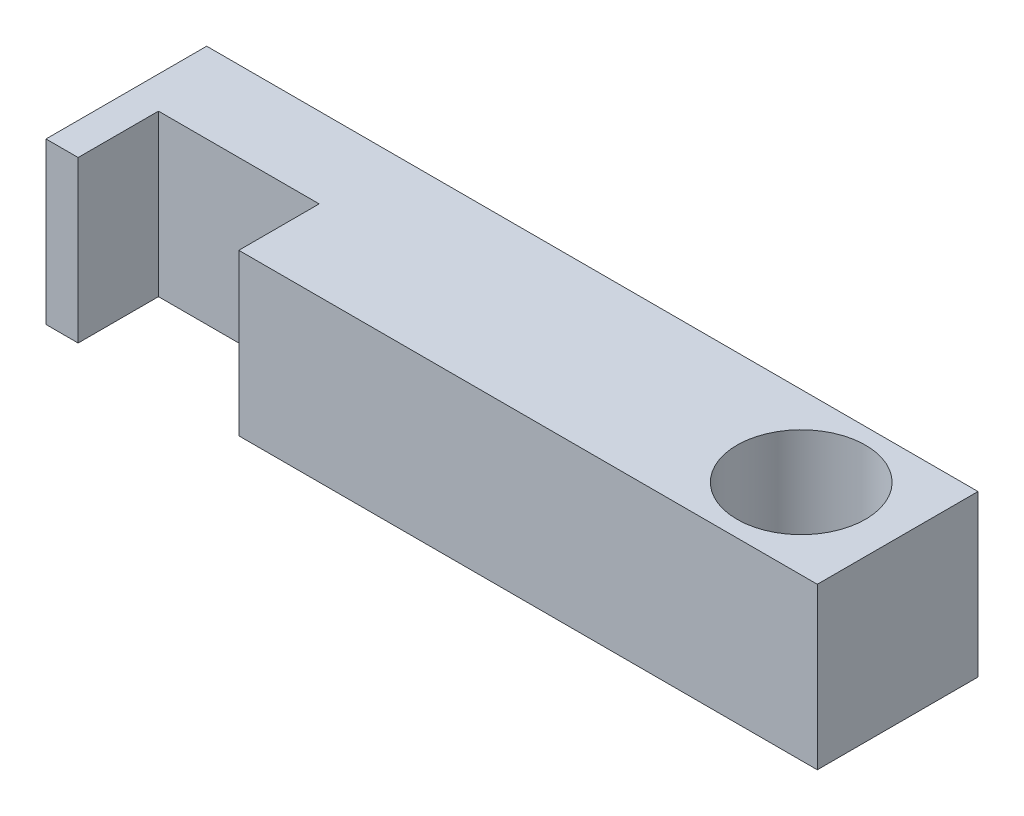
SolidWorks part; units mm, degrees
ref_plane "前基準面" through (0, 0, 0) normal (0, 0, 1) x (1, 0, 0)
ref_plane "上基準面" through (0, 0, 0) normal (0, 1, 0) x (1, 0, 0)
ref_plane "右基準面" through (0, 0, 0) normal (1, 0, 0) x (0, 0, -1)
sketch "草圖1" plane through (0, 0, 0) normal (0, 1, 0) x (1, 0, 0)
  line L0 (-40, -5) -> (-40, 0)
  line L1 (-42, 5) -> (6, 5)
  line L2 (-42, 5) -> (-42, -5)
  line L3 (-42, -5) -> (-40, -5)
  line L4 (6, 5) -> (6, -5)
  line L5 (-40, 0) -> (-30, 0)
  line L6 (-30, 0) -> (-30, -5)
  line L7 (-30, -5) -> (6, -5)
  circle A0 centre (0, 0) radius 4
  point P8 (6, 0)
  dimension "D1" = 6
  dimension "hole" = 8
  dimension "D2" = 10
  dimension "length" = 48
  dimension "D4" = 5
  dimension "D5" = 10
  dimension "D6" = 2
extrude "填料-伸長1" add sketch "草圖1" along normal mid plane 10
